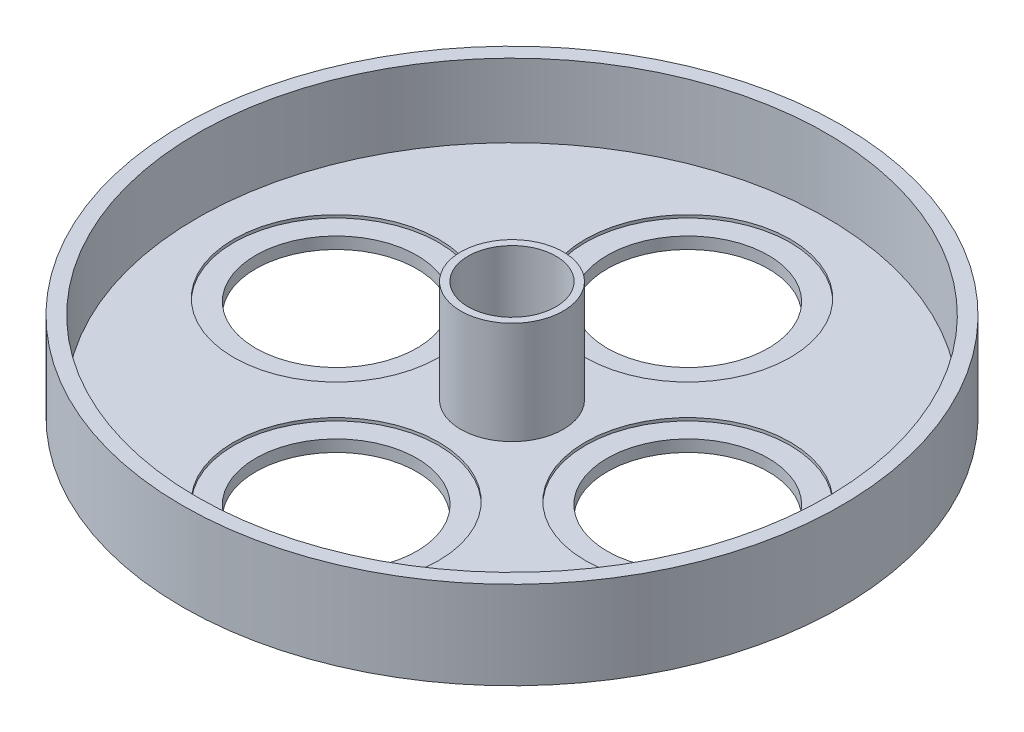
SolidWorks part; units mm, degrees
ref_plane "Alzado" through (0, 0, 0) normal (0, 0, 1) x (1, 0, 0)
ref_plane "Planta" through (0, 0, 0) normal (0, 1, 0) x (1, 0, 0)
ref_plane "Vista lateral" through (0, 0, 0) normal (1, 0, 0) x (0, 0, -1)
sketch "Croquis1" plane through (0, 0, 0) normal (0, 1, 0) x (1, 0, 0)
  circle A0 centre (0, 0) radius 225
  circle A1 centre (0, 0) radius 120 construction
  circle A2 centre (0, 120) radius 55
  circle A9 centre (0, 0) radius 35
  circle A10 centre (120, 0) radius 55
  circle A11 centre (0, -120) radius 55
  circle A12 centre (-120, 0) radius 55
  point P15 (17.5, -17.5)
  point P16 (-12.5, 12.5)
  point P17 (2.5, -2.5)
  point P19 (0, 0)
  dimension "D1" = 450
  dimension "D2" = 240
  dimension "D3" = 110
  dimension "D5" = 70
  dimension "D4" = 4
extrude "Saliente-Extruir1" add sketch "Croquis1" along normal blind 10
sketch "Croquis3" plane through (0, 10, 0) normal (0, 1, 0) x (1, 0, 0)
  circle A1 centre (0, 0) radius 215
  circle A2 centre (0, 0) radius 225 construction
  circle A3 centre (0, 0) radius 225
  dimension "D1" = 430
extrude "Saliente-Extruir2" add sketch "Croquis3" along normal blind 50
sketch "Croquis4" plane through (0, 10, 0) normal (0, 1, 0) x (1, 0, 0)
  circle A0 centre (0, 120) radius 70
  circle A1 centre (0, 0) radius 120 construction
  circle A2 centre (120, 0) radius 70
  circle A3 centre (0, -120) radius 70
  circle A4 centre (-120, 0) radius 70
  point P15 (0, 0)
  dimension "D1" = 140
  dimension "D2" = 4
extrude "Cortar-Extruir2" cut sketch "Croquis4" against normal blind 2
sketch "Croquis5" plane through (0, 10, 0) normal (0, 1, 0) x (1, 0, 0)
  circle A0 centre (0, 0) radius 35 construction
  circle A1 centre (0, 0) radius 35
  circle A2 centre (0, 0) radius 30
  dimension "D1" = 60
extrude "Saliente-Extruir3" add sketch "Croquis5" along normal blind 70 separate body
